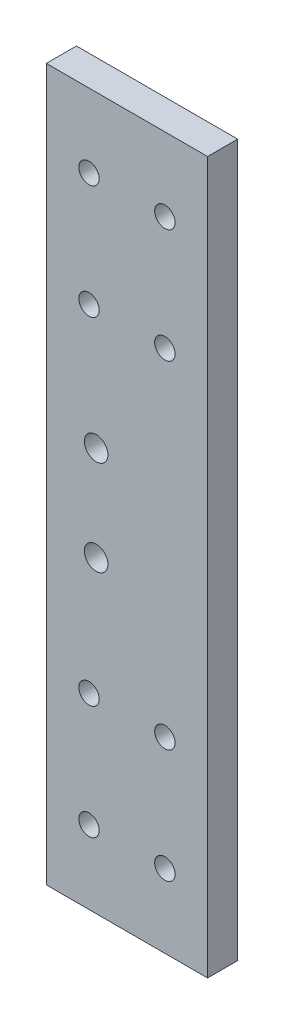
SolidWorks part; units mm, degrees
ref_plane "Front Plane" through (0, 0, 0) normal (0, 0, 1) x (1, 0, 0)
ref_plane "Top Plane" through (0, 0, 0) normal (0, 1, 0) x (1, 0, 0)
ref_plane "Right Plane" through (0, 0, 0) normal (1, 0, 0) x (0, 0, -1)
sketch "Sketch1" plane through (0, 0, 0) normal (0, 0, 1) x (1, 0, 0)
  line L0 (-17, -75) -> (-17, 75)
  line L1 (-17, -75) -> (17, -75)
  line L2 (-17, 75) -> (17, 75)
  line L3 (17, -75) -> (17, 75)
  line L4 (-17, -75) -> (17, 75) construction
  line L5 (-17, 75) -> (17, -75) construction
  point P1 (0, 0)
  dimension "D1" = 34
  dimension "D2" = 150
extrude "Boss-Extrude1" add sketch "Sketch1" along normal blind 6.35
sketch "Sketch4" plane through (0, 0, 6.35) normal (0, 0, 1) x (1, 0, 0)
  line L0 (-8, 35.5) -> (-8, 59.5) construction
  line L1 (-8, 35.5) -> (8, 35.5) construction
  line L2 (-8, 59.5) -> (8, 59.5) construction
  line L3 (8, 35.5) -> (8, 59.5) construction
  line L4 (-8, 35.5) -> (8, 59.5) construction
  line L5 (-8, 59.5) -> (8, 35.5) construction
  line L6 (-8, -35.5) -> (-8, -59.5) construction
  line L7 (-8, -35.5) -> (8, -35.5) construction
  line L8 (-8, -59.5) -> (8, -59.5) construction
  line L9 (8, -35.5) -> (8, -59.5) construction
  line L10 (-8, -35.5) -> (8, -59.5) construction
  line L11 (-8, -59.5) -> (8, -35.5) construction
  line L12 (0, -47.5) -> (0, 47.5) construction
  point P1 (0, 47.5)
  point P2 (0, -47.5)
  point P14 (0, 0)
  dimension "D1" = 24
  dimension "D2" = 16
  dimension "D3" = 24
  dimension "D4" = 16
  dimension "D5" = 95
hole_wizard "#8 Clearance Hole1" positions "Sketch6" profile "Sketch5" hole size "#8" standard "ANSI Inch" end condition through all
sketch "Sketch6" plane through (0, 0, 6.35) normal (0, 0, 1) x (1, 0, 0)
  point P0 (-8, 59.5)
  point P3 (8, 59.5)
  point P6 (8, 35.5)
  point P9 (-8, 35.5)
  point P12 (-8, -35.5)
  point P15 (-8, -59.5)
  point P18 (8, -59.5)
  point P21 (8, -35.5)
sketch "Sketch5" plane through (-8, 59.5, 6.35) normal (1, 0, 0) x (0, -1, 0)
  line L0 (0, 0) -> (0, 6.35)
  line L1 (0, 6.35) -> (2.1526, 6.35)
  line L2 (2.1526, 6.35) -> (2.1526, 0)
  line L5 (2.1526, 0) -> (0, 0)
  line L11 (0, -6.35) -> (0, 107.95) construction
  dimension "Thru Hole Dia." = 4.3053
  dimension "Thru Hole Depth" = 6.35
sketch "Sketch7" plane through (0, 0, 6.35) normal (0, 0, 1) x (1, 0, 0)
  line L0 (-6.5, 10) -> (-6.5, -10) construction
  point P2 (-6.5, 0)
  dimension "D1" = 6.5
  dimension "D2" = 20
hole_wizard "#10 Clearance Hole1" positions "Sketch11" profile "Sketch10" hole size "#10" standard "ANSI Inch" end condition through all
sketch "Sketch11" plane through (0, 0, 6.35) normal (0, 0, 1) x (1, 0, 0)
  point P0 (-6.5, 10)
  point P3 (-6.5, -10)
sketch "Sketch10" plane through (-6.5, 10, 6.35) normal (1, 0, 0) x (0, -1, 0)
  line L0 (0, 0) -> (0, 6.35)
  line L1 (0, 6.35) -> (2.4892, 6.35)
  line L2 (2.4892, 6.35) -> (2.4892, 0)
  line L5 (2.4892, 0) -> (0, 0)
  line L11 (0, -6.35) -> (0, 107.95) construction
  dimension "Thru Hole Dia." = 4.9784
  dimension "Thru Hole Depth" = 6.35
